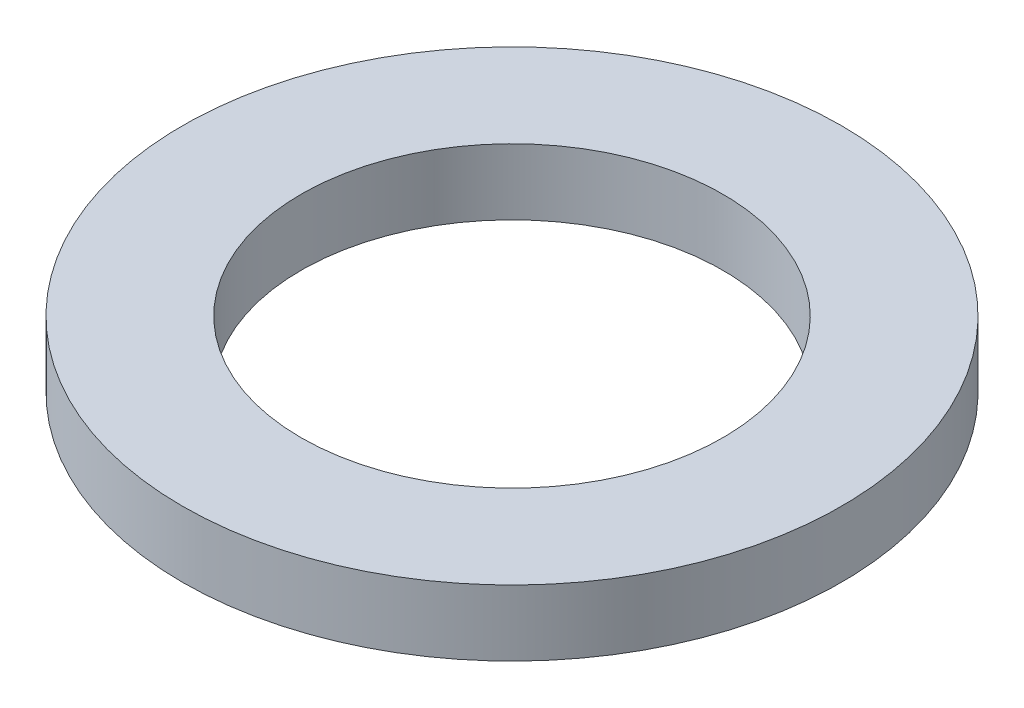
SolidWorks part; units mm, degrees
ref_plane "Płaszczyzna przednia" through (0, 0, 0) normal (0, 0, 1) x (1, 0, 0)
ref_plane "Płaszczyzna górna" through (0, 0, 0) normal (0, 1, 0) x (1, 0, 0)
ref_plane "Płaszczyzna prawa" through (0, 0, 0) normal (1, 0, 0) x (0, 0, -1)
sketch "Sketch1" plane through (0, 0, 0) normal (0, 1, 0) x (1, 0, 0)
  circle A0 centre (0, 0) radius 3.2
  circle A1 centre (0, 0) radius 5
  dimension "D1" = 10
  dimension "D2" = 6.4
extrude "Boss-Extrude1" add sketch "Sketch1" along normal blind 1
